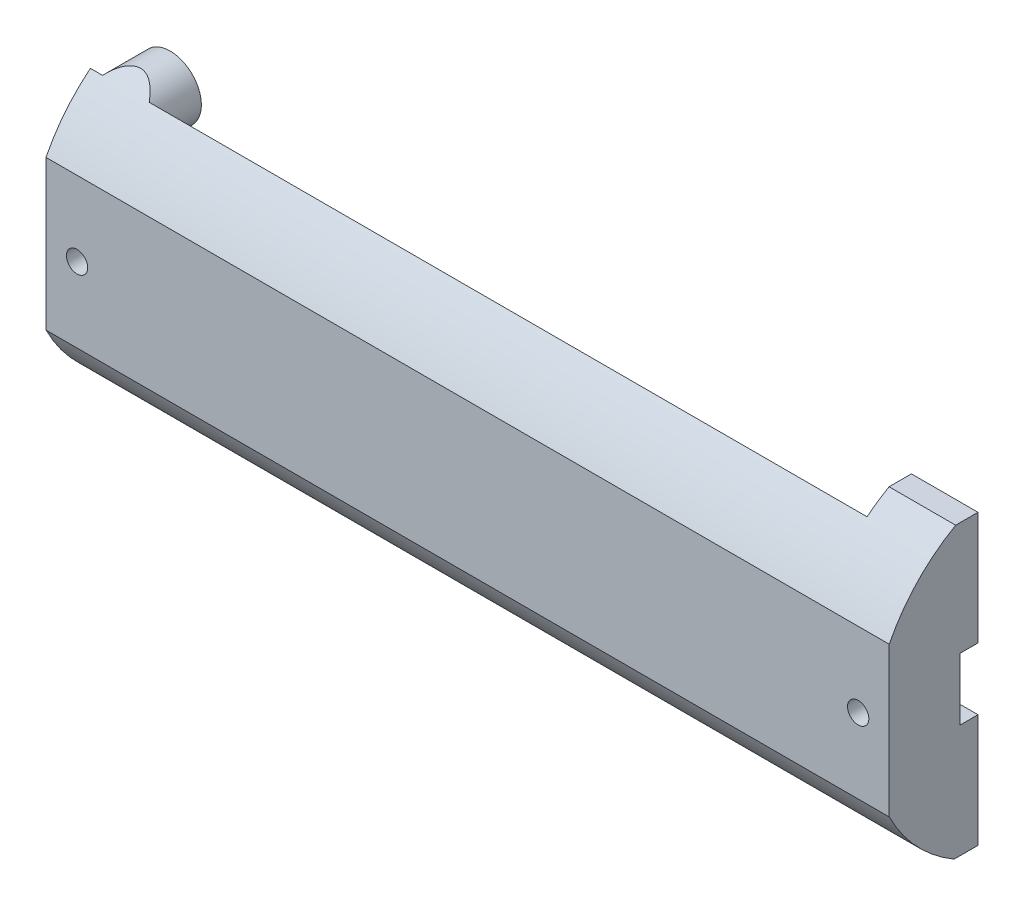
SolidWorks part; units mm, degrees
ref_plane "Front Plane" through (0, 0, 0) normal (0, 0, 1) x (1, 0, 0)
ref_plane "Top Plane" through (0, 0, 0) normal (0, 1, 0) x (1, 0, 0)
ref_plane "Right Plane" through (0, 0, 0) normal (1, 0, 0) x (0, 0, -1)
sketch "Sketch1" plane through (0, 0, 0) normal (0, 0, 1) x (1, 0, 0)
  circle A5 centre (-43.5, -12.25) radius 4
  circle A6 centre (-43.5, -12.25) radius 4
  circle A8 centre (-43.5, 12.25) radius 4
  circle A9 centre (-43.5, 12.25) radius 4
  circle A11 centre (43.5, -12.25) radius 4
  circle A12 centre (43.5, -12.25) radius 4
  circle A14 centre (43.5, 12.25) radius 4
  circle A15 centre (43.5, 12.25) radius 4
  circle A17 centre (-43.5, -12.25) radius 1.5
  circle A18 centre (-43.5, -12.25) radius 1.5
  circle A20 centre (-43.5, 12.25) radius 1.5
  circle A21 centre (-43.5, 12.25) radius 1.5
  circle A23 centre (43.5, -12.25) radius 1.5
  circle A24 centre (43.5, -12.25) radius 1.5
  circle A26 centre (43.5, 12.25) radius 1.5
  circle A27 centre (43.5, 12.25) radius 1.5
  dimension "D1" = 2.5
  dimension "D2" = 2.5
  dimension "D3" = 2.5
  dimension "D4" = 2.5
  dimension "D5" = 0
  dimension "D6" = 0
  dimension "D7" = 0
  dimension "D8" = 0
extrude "Boss-Extrude1" add sketch "Sketch1" along normal blind 5
sketch "Sketch2" plane through (0, 0, 5) normal (0, 0, 1) x (1, 0, 0)
  line L0 (-43.5, 12.25) -> (-43.5, 16.25)
  line L1 (-43.5, 16.25) -> (-47.5, 16.25)
  line L2 (43.5, -12.25) -> (47.5, -12.25)
  line L3 (47.5, -12.25) -> (47.5, -16.25)
  line L5 (-47.5, 16.25) -> (47.5, 16.25)
  line L6 (-47.5, 16.25) -> (-47.5, -16.25)
  line L7 (-47.5, -16.25) -> (47.5, -16.25)
  line L8 (47.5, 16.25) -> (47.5, -16.25)
  circle A2 centre (43.5, 12.25) radius 4
  circle A3 centre (43.5, 12.25) radius 4
  circle A4 centre (43.5, 12.25) radius 4
  circle A5 centre (-43.5, 12.25) radius 4
  circle A6 centre (-43.5, 12.25) radius 4
  circle A9 centre (43.5, -12.25) radius 4
  circle A10 centre (43.5, -12.25) radius 4
  dimension "D1" = 0
  dimension "D2" = 0
  dimension "D3" = 0
  dimension "D4" = 0
extrude "Boss-Extrude2" add sketch "Sketch2" along normal blind 10
sketch "Sketch3" plane through (0, 0, 5) normal (0, 0, -1) x (-1, 0, 0)
  line L0 (0, 16.25) -> (0, -16.25)
  line L1 (43.5, 16.25) -> (-43.5, 16.25) construction
  line L2 (43.5, -16.25) -> (-43.5, -16.25) construction
  line L3 (0, 0) -> (0, 7.1)
  line L4 (0, 7.1) -> (22.5, 7.1)
  line L5 (0, 0) -> (-6.8637, 0)
  line L6 (-22.5, -7.1) -> (22.5, -7.1)
  line L8 (-22.5, -7.1) -> (22.5, -7.1)
  line L9 (-22.5, -7.1) -> (-22.5, 7.1)
  line L10 (-22.5, 7.1) -> (22.5, 7.1)
  line L11 (22.5, -7.1) -> (22.5, 7.1)
  point P13 (0, -7.1)
extrude "Cut-Extrude1" cut sketch "Sketch3" against normal blind 9
sketch "Sketch4" plane through (0, 0, 5) normal (0, 0, -1) x (-1, 0, 0)
  line L2 (-22.5, 7.1) -> (-27.5, 7.1)
  line L3 (22.5, -7.1) -> (27.5, -7.1)
  line L5 (27.5, -7.1) -> (-27.5, -7.1)
  line L6 (27.5, -7.1) -> (27.5, 7.1)
  line L7 (27.5, 7.1) -> (-27.5, 7.1)
  line L8 (-27.5, -7.1) -> (-27.5, 7.1)
extrude "Cut-Extrude2" cut sketch "Sketch4" against normal blind 4 contours L8 L5 L2 M16 | M13 M16 M15 M14 | L6 L7 L3 M14
sketch "Sketch5" plane through (0, 0, 9) normal (0, 0, -1) x (-1, 0, 0)
  circle A2 centre (-24.8, -0.2) radius 1.4
  circle A3 centre (-24.8, -0.2) radius 1.4
  circle A5 centre (24.8, -0.2) radius 1.6
  circle A6 centre (24.8, -0.2) radius 1.6
  dimension "D1" = 0.1
  dimension "D2" = 0.1
extrude "Cut-Extrude3" cut sketch "Sketch5" against normal blind 5
sketch "Sketch6" plane through (0, 0, 5) normal (0, 0, -1) x (-1, 0, 0)
  line L4 (-47.5, 12.25) -> (-47.5, -12.25)
  line L5 (47.5, -12.25) -> (47.5, 12.25)
  line L6 (-39.5, 12.25) -> (-39.5, -12.25)
  line L7 (39.5, 12.25) -> (39.5, -12.25)
  line L8 (-47.5, 12.25) -> (-47.5, -12.25)
  line L9 (-43.5, -16.25) -> (43.5, -16.25)
  line L10 (47.5, -12.25) -> (47.5, 12.25)
  line L11 (43.5, 16.25) -> (-43.5, 16.25)
  line L12 (-47.5, 12.25) -> (-47.5, -12.25)
  line L13 (-43.5, -16.25) -> (43.5, -16.25)
  line L14 (47.5, -12.25) -> (47.5, 12.25)
  line L15 (43.5, 16.25) -> (-43.5, 16.25)
  arc A4 (-47.5, 12.25) -> (-43.5, 16.25) centre (-43.5, 12.25) ccw
  arc A5 (-43.5, -16.25) -> (-47.5, -12.25) centre (-43.5, -12.25) ccw
  arc A6 (47.5, -12.25) -> (43.5, -16.25) centre (43.5, -12.25) ccw
  arc A7 (43.5, 16.25) -> (47.5, 12.25) centre (43.5, 12.25) ccw
  arc A8 (-47.5, 12.25) -> (-43.5, 16.25) centre (-43.5, 12.25) ccw
  arc A9 (-43.5, -16.25) -> (-47.5, -12.25) centre (-43.5, -12.25) ccw
  arc A10 (47.5, -12.25) -> (43.5, -16.25) centre (43.5, -12.25) ccw
  arc A11 (43.5, 16.25) -> (47.5, 12.25) centre (43.5, 12.25) ccw
  arc A12 (-47.5, 12.25) -> (-43.5, 16.25) centre (-43.5, 12.25) ccw
  arc A13 (-43.5, -16.25) -> (-47.5, -12.25) centre (-43.5, -12.25) ccw
  arc A14 (47.5, -12.25) -> (43.5, -16.25) centre (43.5, -12.25) ccw
  arc A15 (43.5, 16.25) -> (47.5, 12.25) centre (43.5, 12.25) ccw
  dimension "D1" = 0
  dimension "D2" = 0
extrude "Boss-Extrude3" add sketch "Sketch6" along normal up to surface (5 mm away) contours L7 M15 M13 M14 | L6 M9 M10 M11 up to face at (47.5, -12.25, 0)
sketch "Sketch8" plane through (47.5, 0, 0) normal (1, 0, 0) x (0, 0, -1)
  line L4 (18.4999, -8.4753) -> (18.4999, 8.377)
  line L5 (-15, 8.377) -> (-15, -8.4753)
  line L6 (18.4999, -8.4753) -> (18.4999, 8.377)
  line L7 (-15, 8.377) -> (-15, -8.4753)
  line L17 (-5, -16.25) -> (-15, -16.25)
  line L18 (-15, -16.25) -> (-15, 16.25)
  line L19 (-15, 16.25) -> (-5, 16.25)
  line L20 (-5, -16.25) -> (-15, -16.25)
  line L21 (-15, -16.25) -> (-15, 16.25)
  line L22 (-15, 16.25) -> (-5, 16.25)
  arc A6 (18.4999, 8.377) -> (-15, 8.377) centre (1.75, -0.0491) ccw
  arc A7 (-15, -8.4753) -> (18.4999, -8.4753) centre (1.75, -0.0491) ccw
  arc A8 (18.4999, 8.377) -> (-15, 8.377) centre (1.75, -0.0491) ccw
  arc A9 (-15, -8.4753) -> (18.4999, -8.4753) centre (1.75, -0.0491) ccw
  dimension "D1" = 2.2
  dimension "D2" = 0
extrude "Cut-Extrude5" cut sketch "Sketch8" against normal through all contours A8 L22 M10 | A9 M10 M11
sketch "Sketch9" plane through (-47.5, 0, 0) normal (-1, 0, 0) x (0, 0, 1)
  line L3 (0, 12.25) -> (0, -12.25) construction
  line L5 (7, 3.5) -> (0, 3.5)
  line L6 (7, 3.5) -> (7, -3.5)
  line L7 (7, -3.5) -> (0, -3.5)
  line L8 (0, 3.5) -> (0, -3.5)
extrude "Cut-Extrude6" cut sketch "Sketch9" against normal through all
sketch "Sketch10" plane through (0, 0, 15) normal (0, 0, 1) x (1, 0, 0)
  line L0 (47.5, -0.0491) -> (44, -0.0491)
  line L1 (47.5, 8.377) -> (47.5, -8.4753) construction
  line L2 (-47.5, -0.0491) -> (-44, -0.0491)
  line L3 (-47.5, 8.377) -> (-47.5, -8.4753) construction
  circle A0 centre (-44, -0.0491) radius 1.2
  circle A1 centre (44, -0.0491) radius 1.2
extrude "Cut-Extrude7" cut sketch "Sketch10" against normal through all
sketch "Sketch12" plane through (0, 0, 0) normal (0, 0, -1) x (-1, 0, 0)
  circle A16 centre (-43.5, 12.25) radius 1.5
  circle A17 centre (-43.5, 12.25) radius 1.5
  circle A19 centre (-43.5, -12.25) radius 1.5
  circle A20 centre (-43.5, -12.25) radius 1.5
  circle A22 centre (43.5, 12.25) radius 1.5
  circle A23 centre (43.5, 12.25) radius 1.5
  circle A25 centre (43.5, -12.25) radius 1.5
  circle A26 centre (43.5, -12.25) radius 1.5
  dimension "D1" = 0
  dimension "D2" = 0
  dimension "D3" = 0
  dimension "D4" = 0
extrude "Cut-Extrude9" cut sketch "Sketch12" against normal blind 10 contours A17 | A20 | A26 | A23
sketch "Sketch13" plane through (0, 0, 0) normal (0, 0, -1) x (-1, 0, 0)
  line L1 (-47.5, 16.25) -> (47.5, 16.25)
  line L2 (-47.5, 16.25) -> (-47.5, -16.25)
  line L3 (-47.5, -16.25) -> (47.5, -16.25)
  line L4 (47.5, 16.25) -> (47.5, -16.25)
extrude "Cut-Extrude10" cut sketch "Sketch13" against normal up to surface (5 mm away) up to face at (0, -8.6857, 5)
sketch "Sketch14" plane through (0, 0, 5) normal (0, 0, -1) x (-1, 0, 0)
  line L0 (-45, -12.25) -> (-40, -12.25)
  line L1 (-40, 16.25) -> (-40, -16.25)
  line L2 (47.5, 16.25) -> (-47.5, 16.25) construction
  line L3 (47.5, -16.25) -> (-47.5, -16.25) construction
  line L5 (-40, 16.25) -> (47.5, 16.25)
  line L6 (-40, 16.25) -> (-40, -16.25)
  line L7 (-40, -16.25) -> (47.5, -16.25)
  line L8 (47.5, 16.25) -> (47.5, -16.25)
  circle A0 centre (-43.5, -12.25) radius 1.5 construction
  circle A1 centre (-43.5, -12.25) radius 1.5 construction
  circle A2 centre (43.5, 12.25) radius 3.5
  circle A3 centre (43.5, -12.25) radius 3.5
extrude "Cut-Extrude11" cut sketch "Sketch14" against normal blind 5 contours L8 L5 L1 A2 M8 M7 M6 M5 M4 | L1 A3 M8 M2 M3 M4 M5 M6 M7
sketch "Sketch15" plane through (0, 0, 14) normal (0, 0, -1) x (-1, 0, 0)
  line L8 (22.5, 7.1) -> (-22.5, 7.1)
  line L9 (-22.5, 7.1) -> (-22.5, -7.1)
  line L10 (-22.5, -7.1) -> (22.5, -7.1)
  line L11 (22.5, -7.1) -> (22.5, 7.1)
  line L12 (22.5, 7.1) -> (-22.5, 7.1)
  line L13 (-22.5, 7.1) -> (-22.5, -7.1)
  line L14 (-22.5, -7.1) -> (22.5, -7.1)
  line L15 (22.5, -7.1) -> (22.5, 7.1)
  dimension "D1" = 0
extrude "Cut-Extrude12" cut sketch "Sketch15" against normal blind 0.5
sketch "Sketch16" plane through (0, 0, 10) normal (0, 0, -1) x (-1, 0, 0)
  line L2 (-27.5, 7.1) -> (-27.5, 7.3)
  line L3 (27.5, -7.1) -> (27.5, -7.3)
  line L5 (-27.5, 7.3) -> (27.5, 7.3)
  line L6 (-27.5, 7.3) -> (-27.5, -7.3)
  line L7 (-27.5, -7.3) -> (27.5, -7.3)
  line L8 (27.5, 7.3) -> (27.5, -7.3)
extrude "Cut-Extrude13" cut sketch "Sketch16" against normal blind 2 contours L8 L5 L2 L6 L7 L3 M22 M21 M11 M8 M9 M10 | M8 M11 M10 M9
